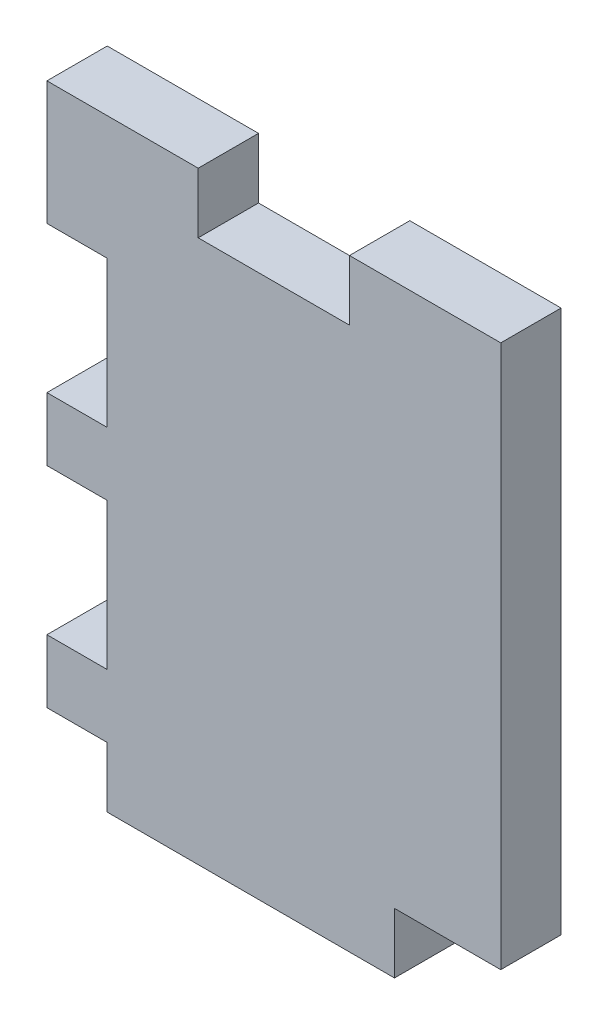
SolidWorks part; units mm, degrees
ref_plane "Front Plane" through (0, 0, 0) normal (0, 0, 1) x (1, 0, 0)
ref_plane "Top Plane" through (0, 0, 0) normal (0, 1, 0) x (1, 0, 0)
ref_plane "Right Plane" through (0, 0, 0) normal (1, 0, 0) x (0, 0, -1)
sketch "Sketch1" plane through (0, 0, 0) normal (0, 0, 1) x (1, 0, 0)
  line L1 (0, 0) -> (40.132, 0)
  line L2 (0, 0) -> (0, 53.34)
  line L3 (0, 53.34) -> (40.132, 53.34)
  line L4 (40.132, 0) -> (40.132, 53.34)
  dimension "D1" = 40.132
  dimension "D2" = 53.34
extrude "Boss-Extrude1" add sketch "Sketch1" along normal blind 5.334 contours L4 L3 L2 L1
sketch "Sketch3" plane through (0, 0, 5.334) normal (0, 0, 1) x (1, 0, 0)
  line L6 (0, 0) -> (5.334, 0)
  line L7 (0, 0) -> (0, 5.334)
  line L8 (0, 5.334) -> (5.334, 5.334)
  line L9 (5.334, 0) -> (5.334, 5.334)
  line L10 (40.132, 0) -> (30.734, 0)
  line L11 (40.132, 0) -> (40.132, 5.334)
  line L12 (40.132, 5.334) -> (30.734, 5.334)
  line L13 (30.734, 0) -> (30.734, 5.334)
  dimension "D1" = 5.334
  dimension "D2" = 5.334
  dimension "D3" = 9.398
  dimension "D4" = 5.334
extrude "Cut-Extrude1" cut sketch "Sketch3" against normal through all contours L7 L6 L9 L8 | L11 L10 L13 L12
sketch "Sketch4" plane through (0, 0, 5.334) normal (0, 0, 1) x (1, 0, 0)
  line L0 (0, 5.334) -> (0, 53.34) construction
  line L1 (0, 42.418) -> (5.334, 42.418)
  line L2 (0, 42.418) -> (0, 29.464)
  line L3 (0, 29.464) -> (5.334, 29.464)
  line L4 (5.334, 42.418) -> (5.334, 29.464)
  line L10 (0, 5.334) -> (5.334, 5.334) construction
  line L11 (0, 10.922) -> (5.334, 10.922)
  line L12 (0, 10.922) -> (0, 23.876)
  line L13 (0, 23.876) -> (5.334, 23.876)
  line L14 (5.334, 10.922) -> (5.334, 23.876)
  dimension "D2" = 5.334
  dimension "D4" = 5.334
  dimension "D1" = 12.954
  dimension "D5" = 12.954
  dimension "D6" = 5.588
  dimension "D3" = 5.588
extrude "Cut-Extrude2" cut sketch "Sketch4" against normal through all contours L2 L1 L4 L3 | L12 L11 L14 L13
sketch "Sketch5" plane through (0, 0, 5.334) normal (0, 0, 1) x (1, 0, 0)
  line L0 (20.066, 53.34) -> (20.066, 0) construction
  line L1 (0, 53.34) -> (40.132, 53.34) construction
  line L2 (5.334, 0) -> (30.734, 0) construction
  line L4 (13.3773, 53.34) -> (26.7547, 53.34)
  line L5 (13.3773, 53.34) -> (13.3773, 48.006)
  line L6 (13.3773, 48.006) -> (26.7547, 48.006)
  line L7 (26.7547, 53.34) -> (26.7547, 48.006)
  dimension "D1" = 5.334
  dimension "D3" = 6.6887
extrude "Cut-Extrude3" cut sketch "Sketch5" against normal through all
equation "\"GMaterial\" = 0.21in"
equation "\"MDF\"= 0.21in"
equation "\"Foamcore\"= 0.2in"
equation "\"D2@Sketch3\"=\"GMaterial\""
equation "\"D4@Sketch3\"=\"GMaterial\""
equation "\"D2@Sketch4\"=\"GMaterial\""
equation "\"D4@Sketch4\"=\"GMaterial\""
equation "\"D1@Boss-Extrude1\"=\"GMaterial\""
equation "\"D2@Sketch1\"=1.68+2*\"GMaterial\""
equation "\"D1@Sketch5\"=\"GMaterial\""
equation "\"D1@Sketch1\"=\"GMaterial\"+1.37"
equation "\"D2@Sketch5\"=(\"GMaterial\"+1.37)/3"
equation "\"D3@Sketch5\"=((\"GMaterial\"+1.37)/3)/2"
equation "\"D1@Sketch3\"=\"GMaterial\""
equation "\"D3@Sketch3\"=(\"GMaterial\"+1.37)-\"GMaterial\"-1"
